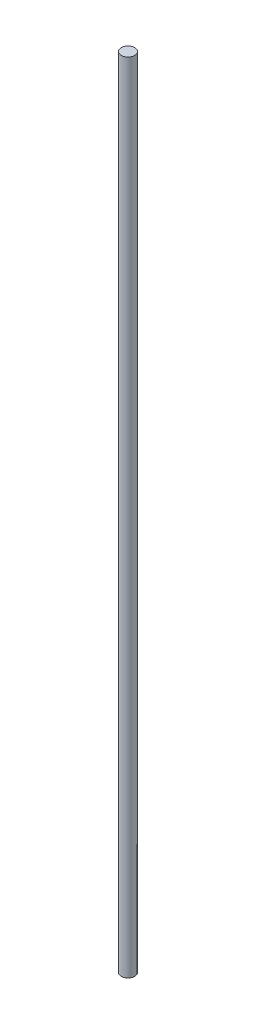
SolidWorks part; units mm, degrees
ref_plane "Front Plane" through (0, 0, 0) normal (0, 0, 1) x (1, 0, 0)
ref_plane "Top Plane" through (0, 0, 0) normal (0, 1, 0) x (1, 0, 0)
ref_plane "Right Plane" through (0, 0, 0) normal (1, 0, 0) x (0, 0, -1)
sketch "Sketch1" plane through (0, 0, 0) normal (0, 1, 0) x (1, 0, 0)
  circle A0 centre (0, 0) radius 4.5
extrude "Boss-Extrude1" add sketch "Sketch1" along normal blind 533
